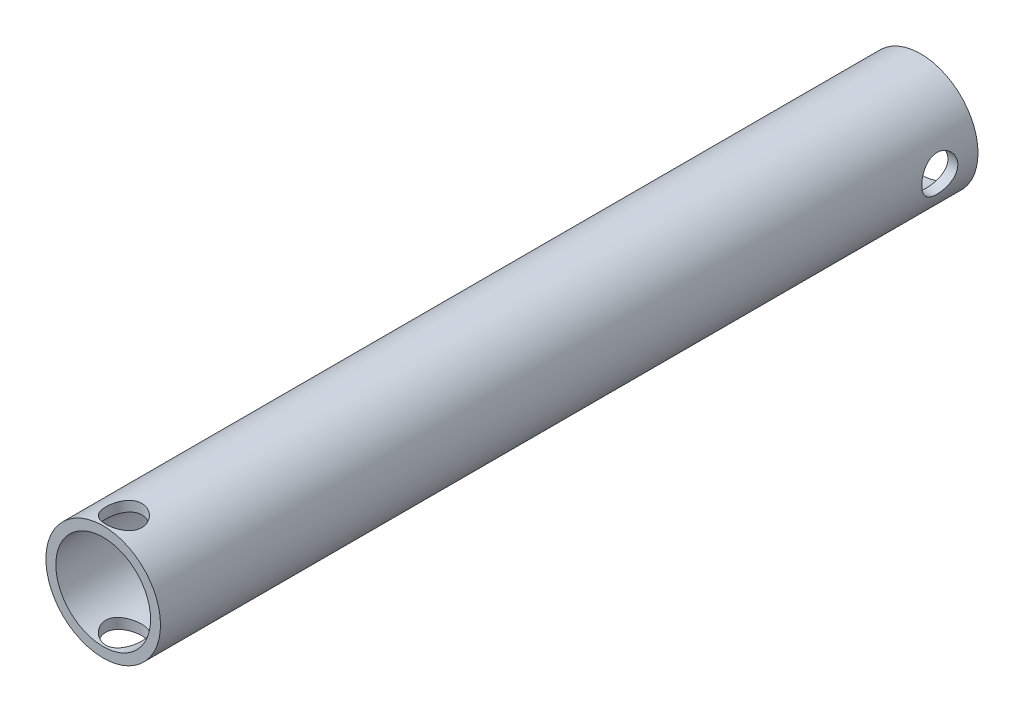
SolidWorks part; units mm, degrees
ref_plane "Front Plane" through (0, 0, 0) normal (0, 0, 1) x (1, 0, 0)
ref_plane "Top Plane" through (0, 0, 0) normal (0, 1, 0) x (1, 0, 0)
ref_plane "Right Plane" through (0, 0, 0) normal (1, 0, 0) x (0, 0, -1)
sketch "Sketch1" plane through (0, 0, 0) normal (0, 0, 1) x (1, 0, 0)
  circle A0 centre (0, 0) radius 9.525
  circle A1 centre (0, 0) radius 7.874
  dimension "D1" = 1.651
extrude "Boss-Extrude1" add sketch "Sketch1" along normal blind 135.89
ref_plane "Plane1" through (0, 9.525, 0) normal (0, 1, 0) x (1, 0, 0)
sketch "Sketch2" plane through (0, 9.525, 0) normal (0, 1, 0) x (1, 0, 0)
  line L0 (-9.525, -67.945) -> (9.525, -67.945) construction
  line L1 (-9.525, 0) -> (-9.525, -135.89) construction
  line L2 (9.525, -135.89) -> (9.525, 0) construction
  line L3 (0, -135.89) -> (0, -132.4559) construction
  line L4 (-9.525, -135.89) -> (9.525, -135.89) construction
  circle A0 centre (0, -132.4559) radius 3
extrude "Cut-Extrude1" cut sketch "Sketch2" against normal blind 138.8059
ref_plane "Plane2" through (9.525, 0, 0) normal (1, 0, 0) x (0, 0, -1)
sketch "Sketch3" plane through (9.525, 0, 0) normal (1, 0, 0) x (0, 0, -1)
  line L0 (0, 0) -> (-6.35, 0) construction
  circle A0 centre (-6.35, 0) radius 3
extrude "Cut-Extrude2" cut sketch "Sketch3" against normal blind 138.8059
